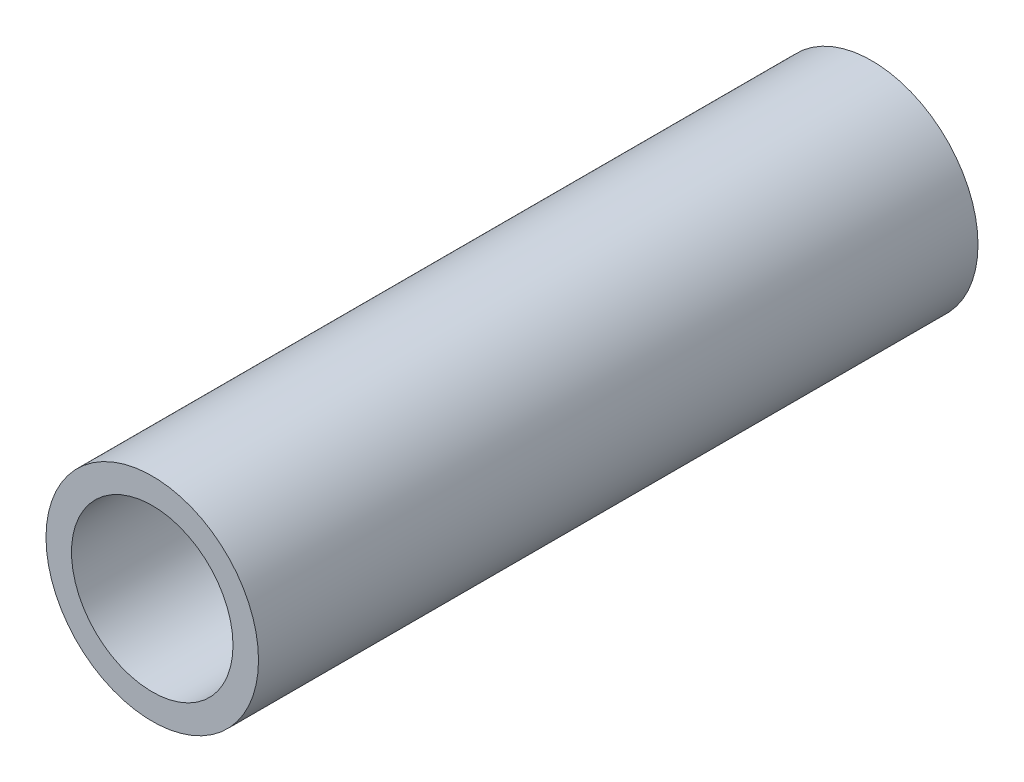
SolidWorks part; units mm, degrees
ref_plane "Front Plane" through (0, 0, 0) normal (0, 0, 1) x (1, 0, 0)
ref_plane "Top Plane" through (0, 0, 0) normal (0, 1, 0) x (1, 0, 0)
ref_plane "Right Plane" through (0, 0, 0) normal (1, 0, 0) x (0, 0, -1)
sketch "Sketch1" plane through (0, 0, 0) normal (0, 0, 1) x (1, 0, 0)
  circle A0 centre (0, 0) radius 3.175
  circle A1 centre (0, 0) radius 2.413
  dimension "D1" = 6.35
  dimension "D2" = 4.826
extrude "Boss-Extrude1" add sketch "Sketch1" along normal mid plane 21.5
